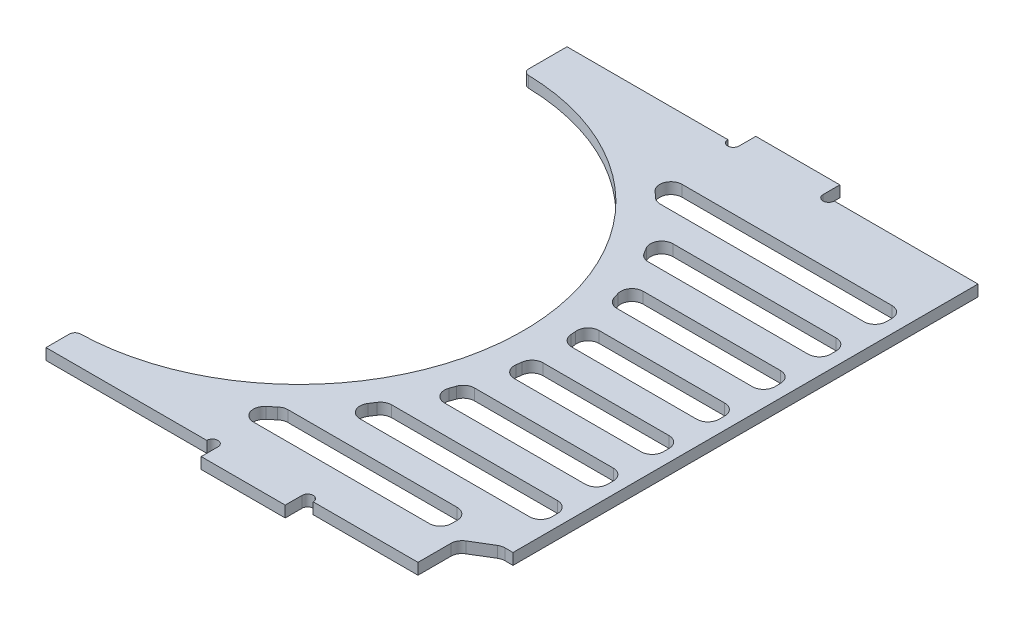
SolidWorks part; units mm, degrees
ref_plane "前视基准面" through (0, 0, 0) normal (0, 0, 1) x (1, 0, 0)
ref_plane "上视基准面" through (0, 0, 0) normal (0, 1, 0) x (1, 0, 0)
ref_plane "右视基准面" through (0, 0, 0) normal (1, 0, 0) x (0, 0, -1)
sketch "草图1" plane through (0, 0, 0) normal (0, 1, 0) x (1, 0, 0)
  line L0 (-38.2, -42.69) -> (-38.2, -45.85)
  line L1 (-38.2, 45.85) -> (38.2, 45.85)
  line L2 (-38.2, 45.85) -> (-38.2, 37.31)
  line L3 (-38.2, -45.85) -> (38.2, -45.85)
  line L4 (38.2, 45.85) -> (38.2, -45.85)
  line L5 (-38.2, 45.85) -> (38.2, -45.85) construction
  line L6 (-38.2, -45.85) -> (38.2, 45.85) construction
  arc A0 (-38.2, -42.69) -> (-38.2, 37.31) centre (-38.2, -2.69) ccw
  point P0 (0, 0)
  dimension "D4" = 80
  dimension "D1" = 91.7
  dimension "80" = 76.4
  dimension "D3" = 48.54
extrude "凸台-拉伸1" add sketch "草图1" along normal blind 2
sketch "草图3" plane through (0, 0, -45.85) normal (0, 0, -1) x (-1, 0, 0)
  line L4 (-38.2, 0) -> (38.2, 0)
  line L5 (38.2, 0) -> (38.2, 2)
  line L6 (38.2, 2) -> (-38.2, 2)
  line L7 (-38.2, 2) -> (-38.2, 0)
  line L8 (-38.2, 0) -> (38.2, 0)
  line L9 (38.2, 0) -> (38.2, 2)
  line L10 (38.2, 2) -> (-38.2, 2)
  line L11 (-38.2, 2) -> (-38.2, 0)
  dimension "D1" = 0
extrude "凸台-拉伸2" add sketch "草图3" along normal blind 7
sketch "草图5" plane through (0, 2, 0) normal (0, 1, 0) x (1, 0, 0)
  line L0 (-38.2, 51.26) -> (38.2, 52.85)
  line L1 (-38.2, 52.85) -> (-38.2, 37.31) construction
  line L2 (38.2, 52.85) -> (-38.2, 52.85)
  line L3 (-38.2, 52.85) -> (-38.2, 51.26)
  dimension "D1" = 1.59
extrude "切除-拉伸1" cut sketch "草图5" against normal blind 10
sketch "草图7" plane through (0, 0, 0) normal (0, -1, 0) x (1, 0, 0)
  line L0 (25.6, -52.5878) -> (25.6, -54.7548)
  line L1 (-38.2, -51.26) -> (38.2, -52.85) construction
  line L2 (25.6, -54.7548) -> (9.6, -54.7548)
  line L3 (9.6, -54.7548) -> (9.6, -52.2548)
  line L4 (9.6, -52.2548) -> (25.6, -52.5878)
  line L5 (38.2, 45.85) -> (38.2, -52.85) construction
  dimension "D1" = 16
  dimension "D2" = 2.5
  dimension "D3" = 12.6
extrude "凸台-拉伸4" add sketch "草图7" against normal blind 2
pattern_linear "阵列(线性)2" count 2 spacing 32 along (-0.9998, 0, 0.0208) of "凸台-拉伸4"
fillet "圆角3" radius 0.5 4 edges at (-22.3931, 1, -54.089) (-6.3931, 1, -54.089) (25.6, 1, -54.7548) (9.6, 1, -54.7548)
sketch "草图10" plane through (0, 2, 0) normal (0, 1, 0) x (1, 0, 0)
  line L2 (-38.8823, 53.9056) -> (39.5858, 55.5386)
  line L3 (39.5858, 55.5386) -> (39.5858, 48.5386)
  line L5 (39.5858, 48.5386) -> (-38.2, 46.9198)
  line L6 (-38.2, 51.26) -> (-38.2, 37.31) construction
  line L10 (-38.8823, 53.9056) -> (-39.2277, 52.8897)
  line L11 (-39.2277, 52.8897) -> (-38.2, 46.9198)
  line L12 (25.6, 52.5878) -> (38.2, 52.85) construction
  dimension "D1" = 7
  dimension "D2" = 180
extrude "切除-拉伸2" cut sketch "草图10" against normal blind 10
sketch "草图11" plane through (0, 2, 0) normal (0, 1, 0) x (1, 0, 0)
  line L0 (-38.2, 46.9198) -> (38.2, 49.5098)
  line L1 (38.2, 49.5098) -> (38.2, 48.5098)
  line L2 (38.2, 48.5098) -> (-38.2, 46.9198)
  dimension "D1" = 1
extrude "凸台-拉伸5" add sketch "草图11" against normal blind 2
sketch "草图13" plane through (0, 0, 0) normal (0, -1, 0) x (1, 0, 0)
  line L0 (38.2, -49.5098) -> (37.7, -49.4928)
  line L1 (38.2, -49.5098) -> (-38.2, -46.9198) construction
  line L2 (37.7, -49.4928) -> (38.2, 45.85)
  line L3 (38.2, 45.85) -> (38.2, -49.5098)
  dimension "D1" = 0.5
extrude "切除-拉伸3" cut sketch "草图13" against normal blind 10
sketch "草图16" plane through (0, 0, 0) normal (0, -1, 0) x (1, 0, 0)
  line L0 (-14.3502, 40.85) -> (33.1737, 40.85)
  line L1 (33.1737, 40.85) -> (32.728, -44.1488)
  line L2 (32.728, -44.1488) -> (-32.4386, -41.9397)
  line L6 (38.2, 45.85) -> (37.7, -49.4928) construction
  line L7 (37.7, -49.4928) -> (-38.2, -46.9198) construction
  line L8 (-38.2, 45.85) -> (38.2, 45.85) construction
  line L9 (37.7542, -39.1488) -> (-21.6316, -39.1488)
  line L10 (37.7542, -34.1488) -> (-21.6316, -34.1488)
  line L11 (37.7542, -29.1488) -> (-21.6316, -29.1488)
  line L12 (37.7542, -24.1488) -> (-21.6316, -24.1488)
  line L13 (37.7542, -19.1488) -> (-21.6316, -19.1488)
  line L14 (37.7542, -14.1488) -> (-21.6316, -14.1488)
  line L15 (37.7542, -9.1488) -> (-21.6316, -9.1488)
  line L16 (37.7542, -4.1488) -> (-21.6316, -4.1488)
  line L17 (37.7542, 0.8512) -> (-21.6316, 0.8512)
  line L18 (37.7542, 5.8512) -> (-21.6316, 5.8512)
  line L19 (37.7542, 10.8512) -> (-21.6316, 10.8512)
  line L20 (37.7542, 15.8512) -> (-21.6316, 15.8512)
  line L21 (37.7542, 20.8512) -> (-21.6316, 20.8512)
  line L22 (37.7542, 25.8512) -> (-21.6316, 25.8512)
  line L23 (37.7542, 30.8512) -> (-21.6316, 30.8512)
  line L24 (37.7542, 35.8512) -> (-21.6316, 35.8512)
  circle A0 centre (-38.2, 2.69) radius 45
  dimension "D3" = 90
  dimension "D1" = 5
  dimension "D2" = 85
  dimension "D4" = 5
  dimension "D5" = 5
  dimension "D6" = 5
extrude "切除-拉伸4" cut sketch "草图16" against normal blind 10 contours A0 L2 L1 L9 | A0 L10 L1 L11 | A0 L12 L1 L13 | A0 L14 L1 L15 | A0 L16 L1 L17 | A0 L18 L1 L19 | A0 L20 L1 L21 | A0 L22 L1 L23 | A0 L24 L1 L0
fillet "圆角5" radius 2 22 edges at (2.9725, 1, 20.8512) (0.3819, 1, 25.8512) (3.5307, 1, -14.1488) (33.0164, 1, 10.8512) (32.9115, 1, -9.1488) (32.9902, 1, 5.8512) (5.2148, 1, -9.1488) (4.8324, 1, 15.8512) (33.1737, 1, 40.85) (-6.3992, 1, -29.1488) (-14.3502, 1, 40.85) (32.8066, 1, -29.1488) (32.7804, 1, -34.1488) (-2.0797, 1, -24.1488) (32.9377, 1, -4.1488) (33.1213, 1, 30.8512) (6.6888, 1, 5.8512) (-3.1009, 1, 30.8512) (32.8853, 1, -14.1488) (-21.6316, 1, -39.1488) (32.7542, 1, -39.1488) (32.728, 1, -44.1488)
sketch "草图23" plane through (0, 0, 0) normal (0, -1, 0) x (1, 0, 0)
  line L3 (30.7437, -39.1488) -> (-21.2543, -39.1488)
  line L4 (32.7387, -42.0907) -> (32.7436, -41.1593)
  line L5 (-32.4386, -41.9397) -> (30.671, -44.0791)
  line L6 (30.7437, -39.1488) -> (-21.2543, -39.1488)
  line L7 (32.7387, -42.0907) -> (32.7436, -41.1593)
  line L8 (-32.4386, -41.9397) -> (30.671, -44.0791)
  arc A4 (-32.4386, -41.9397) -> (-21.9754, -39.2833) centre (-38.2, 2.69) ccw
  arc A5 (-21.2543, -39.1488) -> (-21.9754, -39.2833) centre (-21.2543, -41.1488) ccw
  arc A6 (32.7436, -41.1593) -> (30.7437, -39.1488) centre (30.7437, -41.1488) ccw
  arc A7 (30.671, -44.0791) -> (32.7387, -42.0907) centre (30.7388, -42.0802) ccw
  arc A8 (-32.4386, -41.9397) -> (-21.9754, -39.2833) centre (-38.2, 2.69) ccw
  arc A9 (-21.2543, -39.1488) -> (-21.9754, -39.2833) centre (-21.2543, -41.1488) ccw
  arc A10 (32.7436, -41.1593) -> (30.7437, -39.1488) centre (30.7437, -41.1488) ccw
  arc A11 (30.671, -44.0791) -> (32.7387, -42.0907) centre (30.7388, -42.0802) ccw
  dimension "D1" = 0
extrude "凸台-拉伸9" add sketch "草图23" against normal up to surface (2 mm away) up to face at (-6.15, 2, 0.1112)
fillet "圆角6" radius 2 13 edges at (6.0538, 1, 10.8512) (33.0688, 1, 20.8512) (33.1475, 1, 35.8512) (33.0426, 1, 15.8512) (6.2773, 1, -4.1488) (-12.3562, 1, -34.1488) (1.1455, 1, -19.1488) (-7.7806, 1, 35.8512) (32.9639, 1, 0.8512) (32.8591, 1, -19.1488) (33.0951, 1, 25.8512) (32.8328, 1, -24.1488) (6.7624, 1, 0.8512)
fillet "圆角7" radius 1 3 edges at (-38.2, 1, -37.31) (-38.2, 1, -46.9198) (-38.2, 1, 42.69)
sketch "草图18" plane through (0, 0, 45.85) normal (0, 0, 1) x (1, 0, 0)
  line L4 (-38.2, 0) -> (38.2, 0)
  line L5 (38.2, 0) -> (38.2, 2)
  line L6 (38.2, 2) -> (-38.2, 2)
  line L7 (-38.2, 2) -> (-38.2, 0)
  line L8 (-38.2, 0) -> (38.2, 0)
  line L9 (38.2, 0) -> (38.2, 2)
  line L10 (38.2, 2) -> (-38.2, 2)
  line L11 (-38.2, 2) -> (-38.2, 0)
  dimension "D1" = 0
extrude "凸台-拉伸6" add sketch "草图18" along normal blind 2
sketch "草图19" plane through (0, 2, 0) normal (0, 1, 0) x (1, 0, 0)
  line L1 (38.2, -47.85) -> (28.2, -47.85)
  line L2 (38.2, -47.85) -> (38.2, -37.85)
  line L3 (38.2, -37.85) -> (28.2, -37.85)
  line L4 (28.2, -47.85) -> (28.2, -37.85)
  dimension "D1" = 10
  dimension "D2" = 10
extrude "切除-拉伸5" cut sketch "草图19" against normal through all
sketch "草图20" plane through (0, 2, 0) normal (0, 1, 0) x (1, 0, 0)
  line L1 (-7.012, -35.8512) -> (31.158, -35.8512) construction
  line L2 (25.2, -35.8512) -> (33.158, -35.8512)
  line L3 (33.158, -35.8512) -> (33.158, -37.85)
  line L4 (33.158, -37.85) -> (28.2, -40.85)
  line L5 (25.2, -35.8512) -> (25.2, -40.85)
  line L6 (28.2, -40.85) -> (-8.1758, -40.85) construction
  line L7 (25.2, -40.85) -> (28.2, -40.85)
  dimension "D1" = 1.9988
  dimension "D2" = 3
extrude "凸台-拉伸8" add sketch "草图20" against normal up to surface (2 mm away) up to face at (12.4447, 0, -31.327)
fillet "圆角8" radius 2 2 edges at (25.2, 1, 35.8512) (25.2, 1, 40.85)
fillet "圆角9" radius 2 2 edges at (28.2, 1, 40.85) (33.158, 1, 37.85)
sketch "草图21" plane through (0, 0, 0) normal (0, -1, 0) x (1, 0, 0)
  line L1 (38.158, 37.85) -> (35.158, 37.85)
  line L2 (38.158, 37.85) -> (38.158, -49.4928)
  line L3 (38.158, -49.4928) -> (35.158, -49.4928)
  line L4 (35.158, 37.85) -> (35.158, -49.4928)
  dimension "D1" = 3
  dimension "D2" = 87.3428
extrude "切除-拉伸6" cut sketch "草图21" against normal through all
sketch "草图22" plane through (0, 0, 0) normal (0, -1, 0) x (1, 0, 0)
  line L0 (-39.2441, -47.15) -> (-39.2441, -45.15) construction
  line L1 (-39.2441, -47.15) -> (-31.4091, -47.15) construction
  line L2 (35.158, -49.4067) -> (-37.2339, -46.9525) construction
  line L3 (-39.2441, -45.15) -> (60.7559, -45.15)
  line L4 (60.7559, -45.15) -> (60.7559, -51.15)
  line L5 (60.7559, -51.15) -> (-39.2441, -51.15)
  line L6 (-39.2441, -51.15) -> (-39.2441, -47.15)
  dimension "D1" = 2
  dimension "D2" = 6
  dimension "D3" = 100
extrude "切除-拉伸7" cut sketch "草图22" against normal through all and the other way through all flip side to cut
sketch "草图24" plane through (0, 0, -45.15) normal (0, 0, -1) x (-1, 0, 0)
  line L0 (38.2, 2) -> (-35.158, 2) construction
  line L1 (-7.5, 2) -> (7.5, 2)
  line L2 (-7.5, 2) -> (-7.5, 0)
  line L3 (-7.5, 0) -> (7.5, 0)
  line L4 (7.5, 2) -> (7.5, 0)
  point P7 (0, 2)
  dimension "D1" = 15
  dimension "D2" = 2
extrude "凸台-拉伸10" add sketch "草图24" along normal blind 3
sketch "草图25" plane through (0, 2, 0) normal (0, 1, 0) x (1, 0, 0)
  line L0 (-38.2, 45.15) -> (-7.5, 45.15) construction
  line L1 (7.5, 45.15) -> (35.158, 45.15) construction
  circle A0 centre (-8.5, 45.15) radius 1
  circle A1 centre (8.5, 45.15) radius 1
  dimension "D1" = 2
extrude "切除-拉伸8" cut sketch "草图25" against normal through all
ref_plane "基准面1" through (0, 0, 1.35) normal (0, 0, 1) x (1, 0, 0)
mirror "镜向1" about plane through (0, 0, 1.35) normal (0, 0, 1) of "切除-拉伸8", "凸台-拉伸10"
